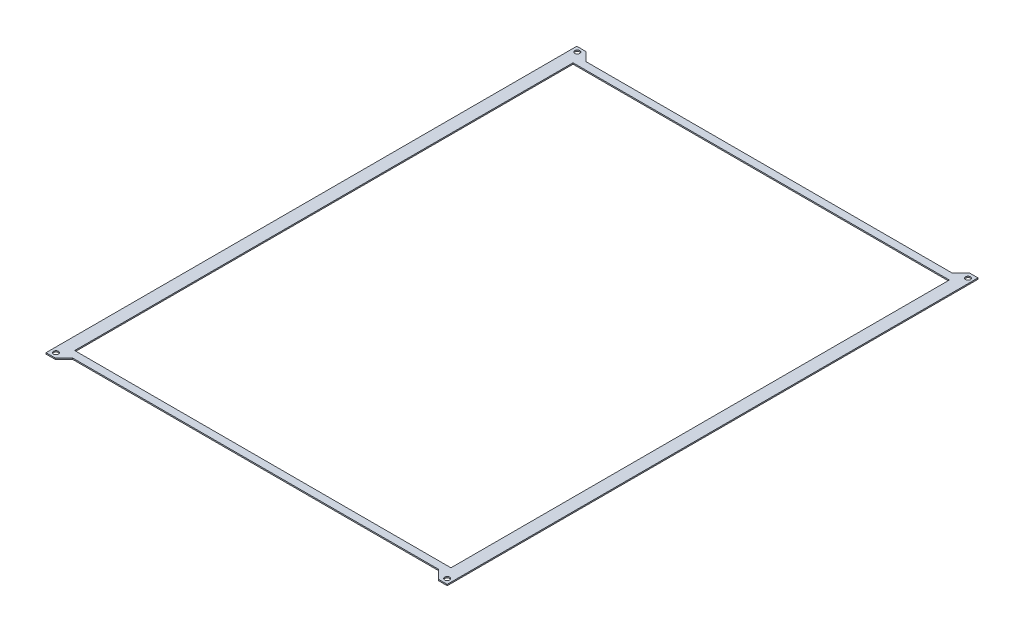
SolidWorks part; units mm, degrees
material "Acero aleado"
ref_plane "Alzado" through (0, 0, 0) normal (0, 0, 1) x (1, 0, 0)
ref_plane "Planta" through (0, 0, 0) normal (0, 1, 0) x (1, 0, 0)
ref_plane "Vista lateral" through (0, 0, 0) normal (1, 0, 0) x (0, 0, -1)
sketch "Croquis1" plane through (0, 0, 0) normal (0, 1, 0) x (1, 0, 0)
  line L0 (73.5, -100) -> (73.5, -106.5) construction
  line L1 (80.5, -106.5) -> (-80.5, -106.5) construction
  line L2 (80.5, -106.5) -> (80.5, 106.5) construction
  line L3 (80.5, 106.5) -> (-80.5, 106.5) construction
  line L4 (-80.5, -106.5) -> (-80.5, 106.5) construction
  line L5 (80.5, -106.5) -> (-80.5, 106.5) construction
  line L6 (80.5, 106.5) -> (-80.5, -106.5) construction
  line L7 (-80.5, -106.4) -> (-80.5, -106.5)
  line L8 (-80.5, -106.5) -> (-80.4, -106.5)
  line L9 (0, 0) -> (-80.5, 0.05) construction
  line L10 (-75.5, 100) -> (75.5, 100)
  line L11 (75.5, -100) -> (-75.5, 100) construction
  line L12 (75.5, 100) -> (-75.5, -100) construction
  line L13 (80.5, -103) -> (-80.5, -103) construction
  line L14 (80.5, -103) -> (80.5, 103) construction
  line L15 (80.5, 103) -> (-80.5, 103) construction
  line L16 (-80.5, -103) -> (-80.5, 103) construction
  line L17 (80.5, -103) -> (-80.5, 103) construction
  line L18 (80.5, 103) -> (-80.5, -103) construction
  line L19 (80.5, -106.5) -> (77, -106.5)
  line L20 (77, -106.5) -> (73.5, -103)
  line L21 (73.5, -103) -> (-73.4, -103)
  line L22 (-73.4, -103) -> (-76.9, -106.5)
  line L23 (-76.9, -106.5) -> (-80.4, -106.5)
  line L24 (-80.5, -106.4) -> (-80.5, 106.5)
  line L25 (-76.9, 106.5) -> (-73.4, 103)
  line L26 (-73.4, 103) -> (73.5, 103)
  line L27 (73.5, 103) -> (77, 106.5)
  line L28 (77, 106.5) -> (80.5, 106.5)
  line L29 (80.5, 106.5) -> (80.5, -106.5)
  line L30 (-80.5, 106.5) -> (-76.9, 106.5)
  line L31 (75.5, 100) -> (75.5, -100)
  line L32 (75.5, -100) -> (-75.5, -100)
  line L33 (-75.5, -100) -> (-75.5, 100)
  circle A0 centre (-78.5, -104.5) radius 1
  circle A1 centre (78.5, -104.5) radius 1
  circle A2 centre (78.6298, 104.4024) radius 1
  circle A3 centre (-78.3701, 104.5974) radius 1
  point P1 (0, 0)
  point P6 (0, 0)
  point P11 (0, 0)
  dimension "D8" = 2
  dimension "D11" = 2
  dimension "D12" = 2
  dimension "D13" = 2
  dimension "D1" = 161
  dimension "D2" = 213
  dimension "D3" = 200
  dimension "D4" = 151
  dimension "D5" = 3.5
  dimension "D6" = 7
  dimension "D7" = 3.5
  dimension "D9" = 2
  dimension "D10" = 2
  dimension "D17" = 3.5
extrude "Saliente-Extruir1" add sketch "Croquis1" along normal blind 0.5
